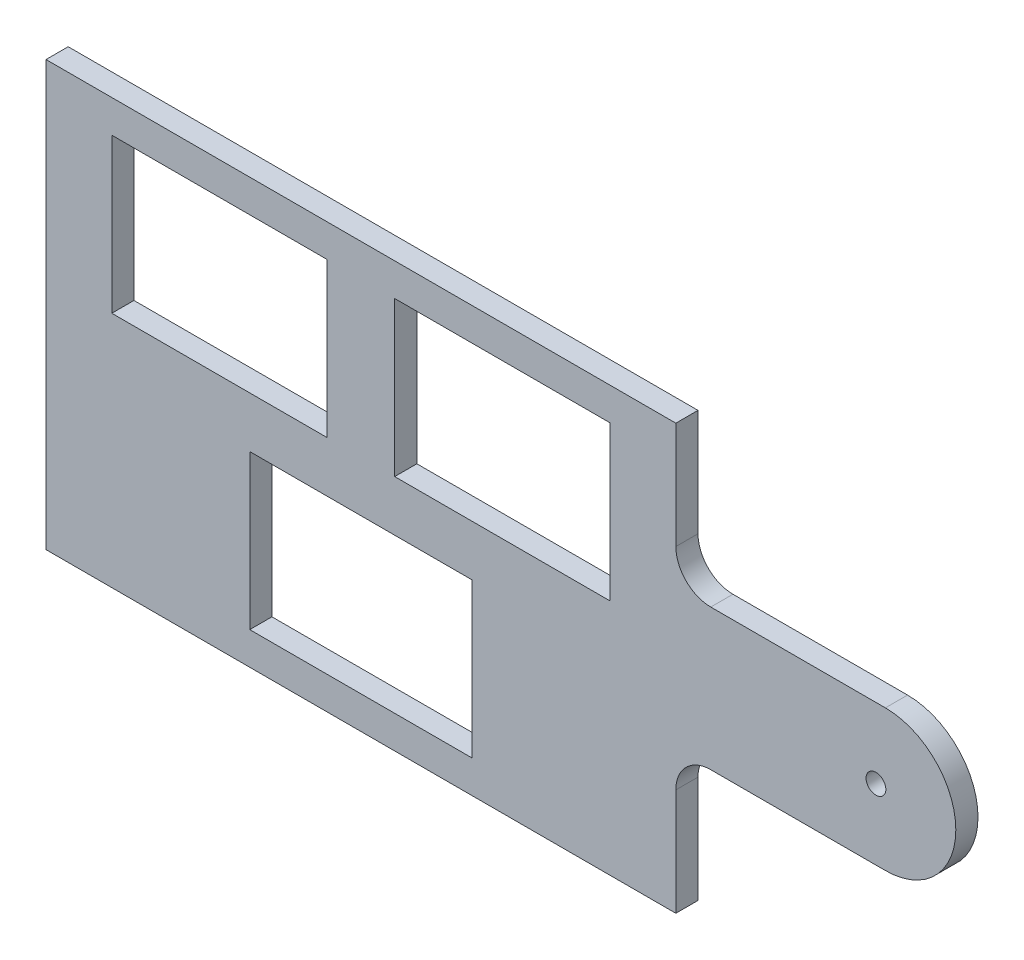
SolidWorks part; units mm, degrees
material "Maple"
ref_plane "Front Plane" through (0, 0, 0) normal (0, 0, 1) x (1, 0, 0)
ref_plane "Top Plane" through (0, 0, 0) normal (0, 1, 0) x (1, 0, 0)
ref_plane "Right Plane" through (0, 0, 0) normal (1, 0, 0) x (0, 0, -1)
sketch "Sketch1" plane through (0, 0, 0) normal (0, 0, 1) x (1, 0, 0)
  line L1 (-45.085, 30.385) -> (45.085, 30.385)
  line L2 (-45.085, 30.385) -> (-45.085, -30.385)
  line L3 (-45.085, -30.385) -> (45.085, -30.385)
  line L4 (45.085, 30.385) -> (45.085, -30.385)
  line L5 (-45.085, 30.385) -> (45.085, -30.385) construction
  line L6 (-45.085, -30.385) -> (45.085, 30.385) construction
  point P0 (0, 0)
  dimension "D1" = 90.17
  dimension "D2" = 60.77
extrude "Boss-Extrude1" add sketch "Sketch1" along normal blind 3.175
sketch "Sketch2" plane through (0, 0, 3.175) normal (0, 0, 1) x (1, 0, 0)
  line L0 (0, 0) -> (-25, 0) construction
  line L5 (-25, 0) -> (-25, -26.8) construction
  line L6 (0, 0) -> (0, -25.8) construction
  line L7 (16, -3.55) -> (-16, -3.55) construction
  line L8 (-16, -3.55) -> (-16, -25.8) construction
  line L9 (-16, -25.8) -> (16, -25.8) construction
  line L10 (16, -3.55) -> (16, -25.8) construction
  line L11 (0, 0) -> (0, 25.8) construction
  line L13 (0, 3.55) -> (-24.5, 3.55) construction
  line L18 (-20.25, 3.55) -> (-20.25, 14.675) construction
  line L19 (35.75, 3.55) -> (4.75, 3.55) construction
  line L23 (-35.75, 25.8) -> (-4.75, 25.8) construction
  line L24 (-35.75, 25.8) -> (-35.75, 3.55) construction
  line L25 (-35.75, 3.55) -> (-4.75, 3.55) construction
  line L26 (-4.75, 25.8) -> (-4.75, 3.55) construction
  line L27 (-35.75, 25.8) -> (-4.75, 3.55) construction
  line L28 (-35.75, 3.55) -> (-4.75, 25.8) construction
  line L29 (4.75, 25.8) -> (4.75, 3.55) construction
  line L30 (35.75, 25.8) -> (4.75, 25.8) construction
  line L31 (35.75, 25.8) -> (35.75, 3.55) construction
  line L32 (35.665, 25.715) -> (4.835, 25.715)
  line L33 (4.835, 25.715) -> (4.835, 3.635)
  line L35 (35.665, 3.635) -> (4.835, 3.635)
  line L36 (35.665, 25.715) -> (35.665, 3.635)
  line L37 (-4.835, 25.715) -> (-4.835, 3.635)
  line L38 (-35.665, 3.635) -> (-4.835, 3.635)
  line L39 (-35.665, 25.715) -> (-35.665, 3.635)
  line L40 (-35.665, 25.715) -> (-4.835, 25.715)
  line L41 (15.915, -3.635) -> (-15.915, -3.635)
  line L42 (-15.915, -3.635) -> (-15.915, -25.715)
  line L43 (-15.915, -25.715) -> (15.915, -25.715)
  line L44 (15.915, -3.635) -> (15.915, -25.715)
  point P0 (0, 0)
  point P3 (0, -3.55)
  point P7 (0, 3.55)
  point P12 (0, -3.55)
  point P14 (-16, 3.55)
  point P17 (0, 14.925)
  point P18 (-20.25, 3.55)
  dimension "D2" = 26.8
  dimension "D3" = 22.25
  dimension "D4" = 16
  dimension "D5" = 7.1
  dimension "D6" = 24.5
  dimension "D7" = 22.25
  dimension "D8" = 8.5
  dimension "D9" = 11.375
  dimension "D10" = 3.55
  dimension "D11" = 4.25
  dimension "D12" = 31
  dimension "D13" = 22.25
  dimension "D14" = 0.085
  dimension "D15" = 0.085
extrude "Cut-Extrude1" cut sketch "Sketch2" against normal through all
sketch "Sketch3" plane through (0, 0, 3.175) normal (0, 0, 1) x (1, 0, 0)
  line L0 (45.085, -30.385) -> (45.085, 30.385) construction
  line L2 (45.085, 10.085) -> (45.085, -10.085)
  line L3 (45.085, 10.085) -> (75.085, 10.085)
  line L4 (45.085, -10.085) -> (75.085, -10.085)
  arc A0 (75.085, 10.085) -> (75.085, -10.085) centre (75.085, 0) cw
  point P5 (45.085, 0)
  dimension "D1" = 20.17
  dimension "D2" = 30
extrude "Boss-Extrude2" add sketch "Sketch3" against normal blind 3.175
fillet "Fillet1" radius 5 2 edges at (45.085, -10.085, 1.5875) (45.085, 10.085, 1.5875)
sketch "Sketch5" plane through (0, 0, 3.175) normal (0, 0, 1) x (1, 0, 0)
  line L0 (0, 0) -> (73.735, 0) construction
  line L1 (50.085, -10.085) -> (75.085, -10.085) construction
  line L2 (45.085, 30.385) -> (-45.085, 30.385) construction
  circle A2 centre (73.735, 0) radius 1.415
  dimension "D1" = 73.735
  dimension "D2" = 2.83
extrude "Cut-Extrude2" cut sketch "Sketch5" against normal blind 10
equation "\"length\"=90"
equation "\"D1@Sketch1\"=\"length\" + 2*\"kerf\""
equation "\"width\"=69.1446"
equation "\"depth\"= 6.35"
equation "\"length2\"= 40.00mm"
equation "\"kerf\"= 0.17 / 2"
